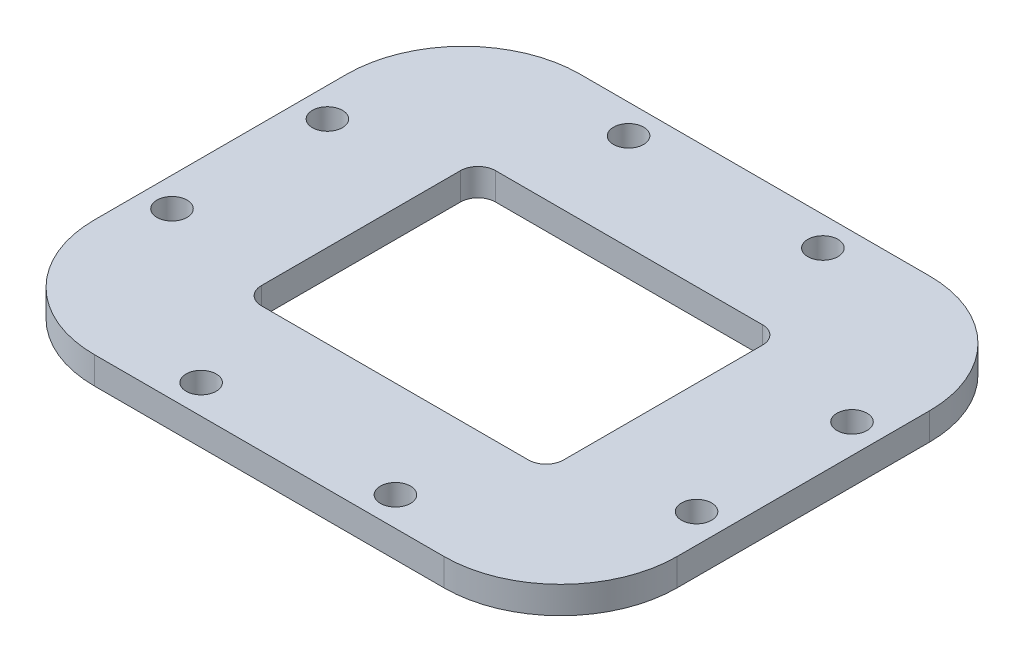
SolidWorks part; units mm, degrees
material "ABS"
ref_plane "前视基准面" through (0, 0, 0) normal (0, 0, 1) x (1, 0, 0)
ref_plane "上视基准面" through (0, 0, 0) normal (0, 1, 0) x (1, 0, 0)
ref_plane "右视基准面" through (0, 0, 0) normal (1, 0, 0) x (0, 0, -1)
other "Configuration Table"
sketch "草图1" plane through (0, 0, 0) normal (0, 1, 0) x (1, 0, 0)
  line L1 (-30, 25) -> (30, 25)
  line L2 (-30, 25) -> (-30, -25)
  line L3 (-30, -25) -> (30, -25)
  line L4 (30, 25) -> (30, -25)
  line L5 (-30, 25) -> (30, -25) construction
  line L6 (-30, -25) -> (30, 25) construction
  line L7 (-14.75, 11.25) -> (14.75, 11.25)
  line L8 (-14.75, 11.25) -> (-14.75, -11.25)
  line L9 (-14.75, -11.25) -> (14.75, -11.25)
  line L10 (14.75, 11.25) -> (14.75, -11.25)
  line L11 (-14.75, 11.25) -> (14.75, -11.25) construction
  line L12 (-14.75, -11.25) -> (14.75, 11.25) construction
  point P0 (0, 0)
  point P6 (0, 0)
  dimension "D1" = 60
  dimension "D2" = 50
  dimension "D3" = 29.5
  dimension "D4" = 22.5
extrude "凸台-拉伸1" add sketch "草图1" along normal blind 2.8
sketch "草图8" plane through (0, 0, 0) normal (0, -1, 0) x (1, 0, 0)
  line L0 (0, 25) -> (0, 0) construction
  line L1 (-30, 25) -> (30, 25) construction
  line L2 (0, 0) -> (30, 0) construction
  line L3 (30, 25) -> (30, -25) construction
  line L4 (-10, 22) -> (10, 22) construction
  circle A0 centre (27, 8) radius 1.55
  circle A1 centre (10, 22) radius 1.55
  circle A2 centre (-10, 22) radius 1.55
  circle A3 centre (-27, 8) radius 1.55
  circle A4 centre (-27, -8) radius 1.55
  circle A5 centre (-10, -22) radius 1.55
  circle A6 centre (10, -22) radius 1.55
  circle A7 centre (27, -8) radius 1.55
  dimension "D1" = 44
  dimension "D2" = 54
  dimension "D3" = 3.1
  dimension "D4" = 20
  dimension "D5" = 16
extrude "切除-拉伸2" cut sketch "草图8" against normal blind 10
fillet "圆角1" radius 1 4 edges at (-14.75, 1.4, 11.25) (14.75, 1.4, 11.25) (14.75, 1.4, -11.25) (-14.75, 1.4, -11.25)
fillet "圆角2" radius 12 4 edges at (30, 1.4, 25) (-30, 1.4, -25) (30, 1.4, -25) (-30, 1.4, 25)
sketch "草图9" plane through (0, 0, 0) normal (0, -1, 0) x (1, 0, 0)
  line L0 (14.75, 10.25) -> (14.75, -10.25) construction
  line L1 (13.75, -11.25) -> (-13.75, -11.25) construction
  line L2 (-14.75, -10.25) -> (-14.75, 10.25) construction
  line L3 (-13.75, 11.25) -> (13.75, 11.25) construction
  line L12 (14.75, 10.25) -> (14.75, -10.25) construction
  line L13 (13.75, -11.25) -> (-13.75, -11.25) construction
  line L14 (-14.75, -10.25) -> (-14.75, 10.25) construction
  line L15 (-13.75, 11.25) -> (13.75, 11.25) construction
  line L16 (-13.75, 12.05) -> (13.75, 12.05)
  line L17 (-15.55, -10.25) -> (-15.55, 10.25)
  line L18 (13.75, -12.05) -> (-13.75, -12.05)
  line L19 (15.55, 10.25) -> (15.55, -10.25)
  arc A0 (14.75, 10.25) -> (13.75, 11.25) centre (13.75, 10.25) ccw construction
  arc A1 (13.75, -11.25) -> (14.75, -10.25) centre (13.75, -10.25) ccw construction
  arc A2 (-14.75, -10.25) -> (-13.75, -11.25) centre (-13.75, -10.25) ccw construction
  arc A3 (-13.75, 11.25) -> (-14.75, 10.25) centre (-13.75, 10.25) ccw construction
  arc A12 (14.75, 10.25) -> (13.75, 11.25) centre (13.75, 10.25) ccw construction
  arc A13 (13.75, -11.25) -> (14.75, -10.25) centre (13.75, -10.25) ccw construction
  arc A14 (-14.75, -10.25) -> (-13.75, -11.25) centre (-13.75, -10.25) ccw construction
  arc A15 (-13.75, 11.25) -> (-14.75, 10.25) centre (-13.75, 10.25) ccw construction
  arc A16 (15.55, 10.25) -> (13.75, 12.05) centre (13.75, 10.25) ccw
  arc A17 (-13.75, 12.05) -> (-15.55, 10.25) centre (-13.75, 10.25) ccw
  arc A18 (-15.55, -10.25) -> (-13.75, -12.05) centre (-13.75, -10.25) ccw
  arc A19 (13.75, -12.05) -> (15.55, -10.25) centre (13.75, -10.25) ccw
  dimension "D1" = 0.8
extrude "切除-拉伸3" cut sketch "草图9" against normal blind 10
